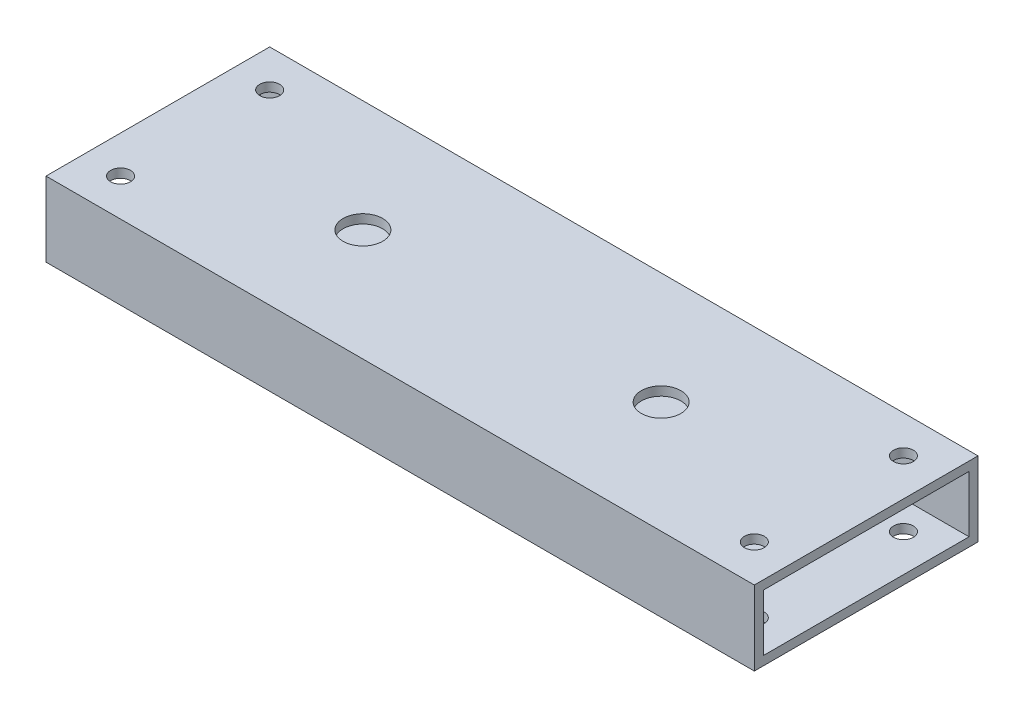
SolidWorks part; units mm, degrees
material "Plain Carbon Steel"
ref_plane "Front Plane" through (0, 0, 0) normal (0, 0, 1) x (1, 0, 0)
ref_plane "Top Plane" through (0, 0, 0) normal (0, 1, 0) x (1, 0, 0)
ref_plane "Right Plane" through (0, 0, 0) normal (1, 0, 0) x (0, 0, -1)
sketch "Sketch1" plane through (0, 0, 0) normal (0, 1, 0) x (1, 0, 0)
  line L0 (120.65, 0) -> (-120.65, 0)
  point P4 (0, 0)
  dimension "D1" = 241.3
other "Rectangular tube 1.5 X 3 X .125(1)"
ref_plane "Plane1" through (120.65, 0, 0) normal (-1, 0, 0) x (0, 0, 1)
sketch "Sketch11" plane through (120.65, 0, 0) normal (-1, 0, 0) x (0, 0, 1)
  line L0 (-35.052, 9.652) -> (35.052, 9.652)
  line L1 (-38.1, -12.7) -> (38.1, -12.7)
  line L2 (-38.1, -12.7) -> (-38.1, 12.7)
  line L3 (-38.1, 12.7) -> (38.1, 12.7)
  line L4 (38.1, -12.7) -> (38.1, 12.7)
  line L5 (-38.1, -12.7) -> (38.1, 12.7) construction
  line L6 (-38.1, 12.7) -> (38.1, -12.7) construction
  line L7 (35.052, -9.652) -> (35.052, 9.652)
  line L8 (-35.052, -9.652) -> (35.052, -9.652)
  line L9 (-35.052, -9.652) -> (-35.052, 9.652)
  point P0 (0, 0)
  point P10 (0, 0)
  dimension "D1" = 76.2
  dimension "D2" = 25.4
  dimension "D3" = 3.048
sketch "Sketch12" plane through (0, -12.7, 0) normal (0, -1, 0) x (1, 0, 0)
  line L0 (50.8, 0) -> (-50.8, 0)
  point P4 (0, 0)
  dimension "D1" = 101.6
hole_wizard "CBORE for 1/2 Hex Head Bolt1" positions "Sketch13" profile "Sketch14" counterbore size "1/2" standard "ANSI Inch" end condition through all
sketch "Sketch13" plane through (0, -12.7, 0) normal (0, -1, 0) x (-1, 0, 0)
  point P0 (50.8, 0)
  point P3 (-50.8, 0)
sketch "Sketch14" plane through (-50.8, -12.7, 0) normal (1, 0, 0) x (0, 0, -1)
  line L0 (0, 0) -> (0, 25.4)
  line L1 (0, 25.4) -> (6.7462, 25.4)
  line L3 (6.7462, 25.4) -> (6.7462, 3.175)
  line L4 (6.7462, 3.175) -> (14.2875, 3.175)
  line L5 (14.2875, 3.175) -> (14.2875, 0)
  line L7 (14.2875, 0) -> (0, 0)
  line L11 (0, -6.35) -> (0, 107.95) construction
  dimension "Thru Hole Dia." = 13.4925
  dimension "Thru Hole Depth" = 25.4
  dimension "C'Bore Dia." = 28.575
  dimension "C'Bore Depth" = 3.175
sketch "Sketch15" plane through (0, -12.7, 0) normal (0, -1, 0) x (1, 0, 0)
  line L0 (-120.65, 38.1) -> (120.65, 38.1) construction
  line L1 (107.95, 25.4) -> (-107.95, 25.4)
  line L2 (107.95, 25.4) -> (107.95, -25.4)
  line L3 (107.95, -25.4) -> (-107.95, -25.4)
  line L4 (-107.95, 25.4) -> (-107.95, -25.4)
  line L5 (107.95, 25.4) -> (-107.95, -25.4) construction
  line L6 (107.95, -25.4) -> (-107.95, 25.4) construction
  line L7 (-120.65, -38.1) -> (-120.65, 38.1) construction
  point P0 (0, 0)
  dimension "D1" = 12.7
  dimension "D2" = 12.7
hole_wizard "1/4 Clearance Hole1" positions "Sketch16" profile "Sketch17" hole size "1/4" standard "ANSI Inch" end condition through all
sketch "Sketch16" plane through (0, -12.7, 0) normal (0, -1, 0) x (-1, 0, 0)
  point P0 (107.95, -25.4)
  point P3 (107.95, 25.4)
  point P6 (-107.95, 25.4)
  point P9 (-107.95, -25.4)
sketch "Sketch17" plane through (-107.95, -12.7, 25.4) normal (1, 0, 0) x (0, 0, -1)
  line L0 (0, 0) -> (0, 25.4)
  line L1 (0, 25.4) -> (3.3782, 25.4)
  line L2 (3.3782, 25.4) -> (3.3782, 0)
  line L5 (3.3782, 0) -> (0, 0)
  line L11 (0, -6.35) -> (0, 107.95) construction
  dimension "Thru Hole Dia." = 6.7564
  dimension "Thru Hole Depth" = 25.4
